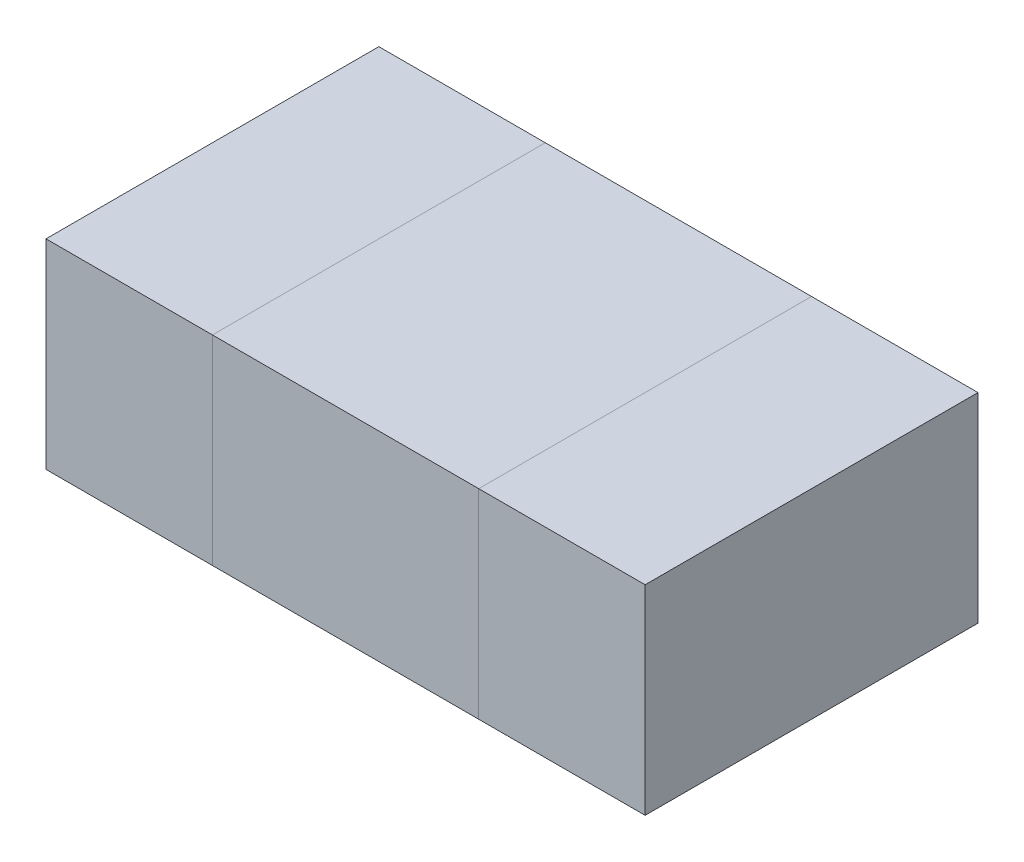
SolidWorks part; units mm, degrees
ref_plane "Front Plane" through (0, 0, 0) normal (0, 0, 1) x (1, 0, 0)
ref_plane "Top Plane" through (0, 0, 0) normal (0, 1, 0) x (1, 0, 0)
ref_plane "Right Plane" through (0, 0, 0) normal (1, 0, 0) x (0, 0, -1)
sketch "Sketch1" plane through (0, 0, 0) normal (0, 1, 0) x (1, 0, 0)
  line L1 (-0.2, -0.25) -> (0.2, -0.25)
  line L2 (-0.2, -0.25) -> (-0.2, 0.25)
  line L3 (-0.2, 0.25) -> (0.2, 0.25)
  line L4 (0.2, -0.25) -> (0.2, 0.25)
  line L5 (-0.2, -0.25) -> (0.2, 0.25) construction
  line L6 (-0.2, 0.25) -> (0.2, -0.25) construction
  point P0 (0, 0)
  dimension "D1" = 0.4
  dimension "D2" = 0.5
extrude "Boss-Extrude1" add sketch "Sketch1" along normal blind 0.3
sketch "Sketch2" plane through (0, 0, 0) normal (0, 1, 0) x (1, 0, 0)
  line L0 (0, 0.25) -> (0, -0.25) construction
  line L1 (-0.2, 0.25) -> (-0.45, 0.25)
  line L2 (-0.2, 0.25) -> (-0.2, -0.25)
  line L3 (-0.2, -0.25) -> (-0.45, -0.25)
  line L4 (-0.45, 0.25) -> (-0.45, -0.25)
  line L5 (0.2, 0.25) -> (-0.2, 0.25) construction
  line L6 (-0.2, -0.25) -> (0.2, -0.25) construction
  line L7 (0.2, -0.25) -> (0.45, -0.25)
  line L8 (0.45, 0.25) -> (0.45, -0.25)
  line L9 (0.2, 0.25) -> (0.45, 0.25)
  line L10 (0.2, 0.25) -> (0.2, -0.25)
  dimension "D1" = 0.5
  dimension "D2" = 0.25
extrude "Boss-Extrude2" add sketch "Sketch2" along normal blind 0.3 separate body
